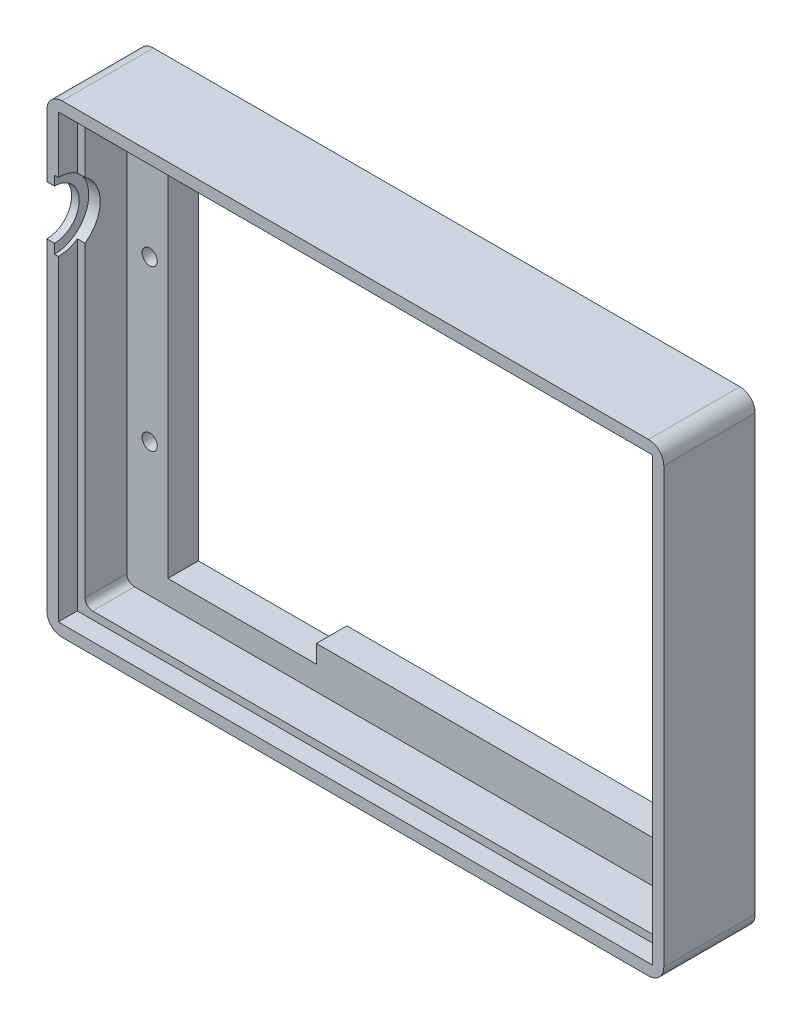
SolidWorks part; units mm, degrees
ref_plane "Plan de face" through (0, 0, 0) normal (0, 0, 1) x (1, 0, 0)
ref_plane "Plan de dessus" through (0, 0, 0) normal (0, 1, 0) x (1, 0, 0)
ref_plane "Plan de droite" through (0, 0, 0) normal (1, 0, 0) x (0, 0, -1)
sketch "Esquisse1" plane through (0, 0, 0) normal (0, 0, 1) x (1, 0, 0)
  line L1 (0, 0) -> (65, 0)
  line L2 (0, 0) -> (0, 45)
  line L3 (0, 45) -> (65, 45)
  line L4 (65, 0) -> (65, 45)
  dimension "D1" = 45
  dimension "D2" = 65
extrude "Extru.-Mince1" add sketch "Esquisse1" along normal blind 4 thin
sketch "Esquisse3" plane through (0, 0, 0) normal (0, 0, 1) x (1, 0, 0)
  line L0 (-2.5, 49.0311) -> (-2.5, 6.6902) construction
  line L3 (-17.3996, 12) -> (112.1515, 12) construction
  line L5 (67.5, 47.1098) -> (67.5, 5.3461) construction
  line L8 (32.5, 61.6241) -> (32.5, -20.1608) construction
  line L9 (73, -8) -> (73, 53) construction
  line L10 (-8, 53) -> (-8, -8) construction
  line L11 (-26.8181, 22.5) -> (107.1053, 22.5) construction
  line L12 (73, 53) -> (-8, 53) construction
  line L13 (-8, -8) -> (73, -8) construction
  line L14 (9.64, 37.0819) -> (9.64, 61.135) construction
  line L15 (-0.11, 47.36) -> (19.39, 47.36)
  line L16 (-0.11, 47.36) -> (-0.11, 43.36)
  line L18 (19.39, 47.36) -> (19.39, 43.36)
  line L19 (20.1073, 45.36) -> (-23.111, 45.36) construction
  line L22 (-0.11, 1.64) -> (-0.11, -2.36)
  line L23 (-0.11, -2.36) -> (19.39, -2.36)
  line L24 (19.39, 1.64) -> (19.39, -2.36)
  line L25 (-0.11, 43.36) -> (-0.11, 1.64)
  line L26 (19.39, 43.36) -> (19.39, 1.64)
  circle A0 centre (-2.5, 33) radius 1
  circle A1 centre (-2.5, 12) radius 1
  circle A2 centre (67.5, 33) radius 1
  circle A3 centre (67.5, 12) radius 1
  dimension "D1" = 2
  dimension "D4" = 2
  dimension "D5" = 2
  dimension "D2" = 21
  dimension "D3" = 70
  dimension "D6" = 21
  dimension "D7" = 19.5
  dimension "D8" = 4
  dimension "D9" = 22.86
  dimension "D10" = 22.86
extrude "Enlèv. mat.-Extru.1" cut sketch "Esquisse3" along normal blind 13
sketch "Esquisse4" plane through (0, 0, 0) normal (0, 0, 1) x (1, 0, 0)
  line L1 (-8, 53) -> (73, 53)
  line L2 (-8, 53) -> (-8, -8)
  line L3 (-8, -8) -> (73, -8)
  line L4 (73, 53) -> (73, -8)
extrude "Extru.-Mince2" add sketch "Esquisse4" along normal blind 12 thin
ref_plane "face g" through (-5.5, 0, 0) normal (1, 0, 0) x (0, 0, -1)
sketch "Esquisse6" plane through (-5.5, 0, 0) normal (1, 0, 0) x (0, 0, -1)
  line L4 (-12, 44.053) -> (-12, 35.053)
  line L5 (-12, 50.5) -> (-12, -5.5) construction
  arc A1 (-12, 44.053) -> (-12, 35.053) centre (-12, 39.553) cw
  point P0 (-12, 39.553)
  point P4 (0, 0)
  point P5 (0, 0)
  point P6 (0, 0)
  dimension "D1" = 4.5
  dimension "D2" = 0
sketch "Esquisse7" plane through (-5.5, 0, 0) normal (1, 0, 0) x (0, 0, -1)
  line L0 (-12, 50.5) -> (-12, -5.5) construction
  line L2 (-12, 42.803) -> (-12, 36.303)
  arc A2 (-12, 36.303) -> (-12, 42.803) centre (-12, 39.553) ccw
  point P2 (0, 0)
  point P4 (0, 0)
  point P7 (0, 0)
  point P8 (0, 0)
  point P9 (0, 0)
  point P10 (-15, 26.659)
  point P11 (0, 0)
  point P12 (-15, 29.1688)
  point P13 (0, 0)
  point P14 (-15, 39.553)
  dimension "D2" = 0
  dimension "D1" = 6.5
extrude "Enlèv. mat.-Extru.5" cut sketch "Esquisse7" against normal blind 11.5
extrude "Enlèv. mat.-Extru.4" cut sketch "Esquisse6" against normal blind 1.5
ref_plane "Plan1" through (0, 0, 12) normal (0, 0, 1) x (1, 0, 0)
sketch "Esquisse9" plane through (0, 0, 12) normal (0, 0, 1) x (1, 0, 0)
  line L0 (70.5, 50.5) -> (-5.5, 50.5) construction
  line L1 (-5.5, 50.5) -> (70.5, 50.5)
  line L2 (-5.5, 50.5) -> (-5.5, -5.5)
  line L3 (-5.5, -5.5) -> (70.5, -5.5)
  line L4 (70.5, 50.5) -> (70.5, -5.5)
  line L5 (-5.5, -5.5) -> (70.5, -5.5) construction
  line L6 (70.5, -5.5) -> (70.5, 50.5) construction
  line L7 (-5.5, -2.75) -> (-5.5, 2.75) construction
extrude "Enlèv. de mat.-Extru.-Mince1" cut sketch "Esquisse9" against normal blind 2.5 thin thin type one direction wall 1
fillet "Congé4" radius 1 4 edges at (-5.5, -5.5, 6.75) (70.5, -5.5, 6.75) (70.5, 50.5, 6.75) (-5.5, 50.5, 6.75)
fillet "Congé5" radius 2 4 edges at (-8, 53, 6) (73, 53, 6) (73, -8, 6) (-8, -8, 6)
